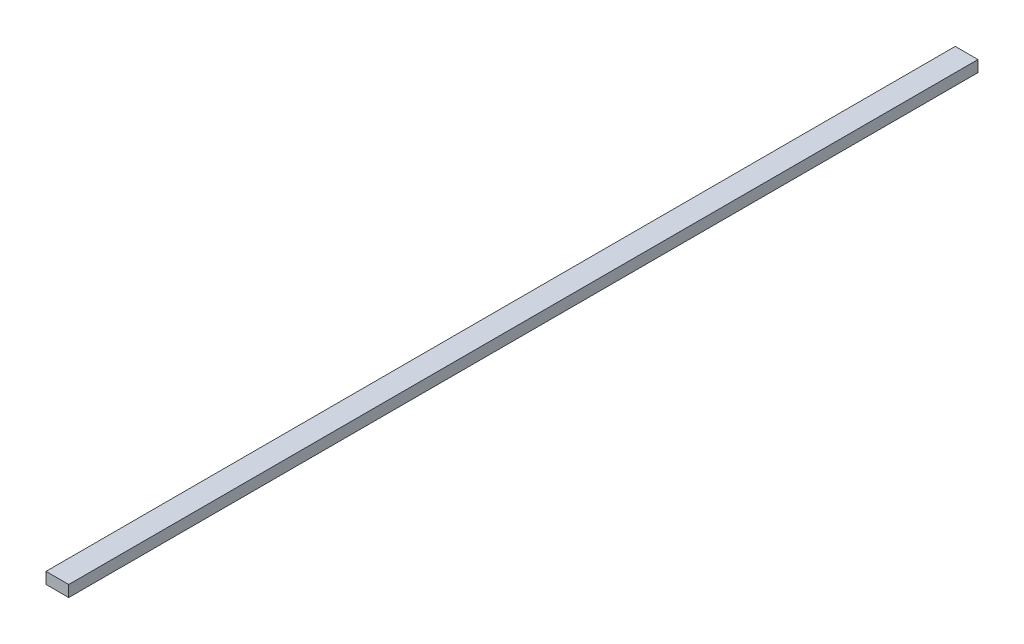
SolidWorks part; units mm, degrees
ref_plane "Front Plane" through (0, 0, 0) normal (0, 0, 1) x (1, 0, 0)
ref_plane "Top Plane" through (0, 0, 0) normal (0, 1, 0) x (1, 0, 0)
ref_plane "Right Plane" through (0, 0, 0) normal (1, 0, 0) x (0, 0, -1)
sketch "Sketch1" plane through (0, 0, 0) normal (0, 0, 1) x (1, 0, 0)
  line L1 (-6.25, -3.125) -> (6.25, -3.125)
  line L2 (-6.25, -3.125) -> (-6.25, 3.125)
  line L3 (-6.25, 3.125) -> (6.25, 3.125)
  line L4 (6.25, -3.125) -> (6.25, 3.125)
  line L5 (-6.25, -3.125) -> (6.25, 3.125) construction
  line L6 (-6.25, 3.125) -> (6.25, -3.125) construction
  point P0 (0, 0)
  dimension "D1" = 12.5
  dimension "D2" = 6.25
extrude "Boss-Extrude1" add sketch "Sketch1" along normal blind 500
